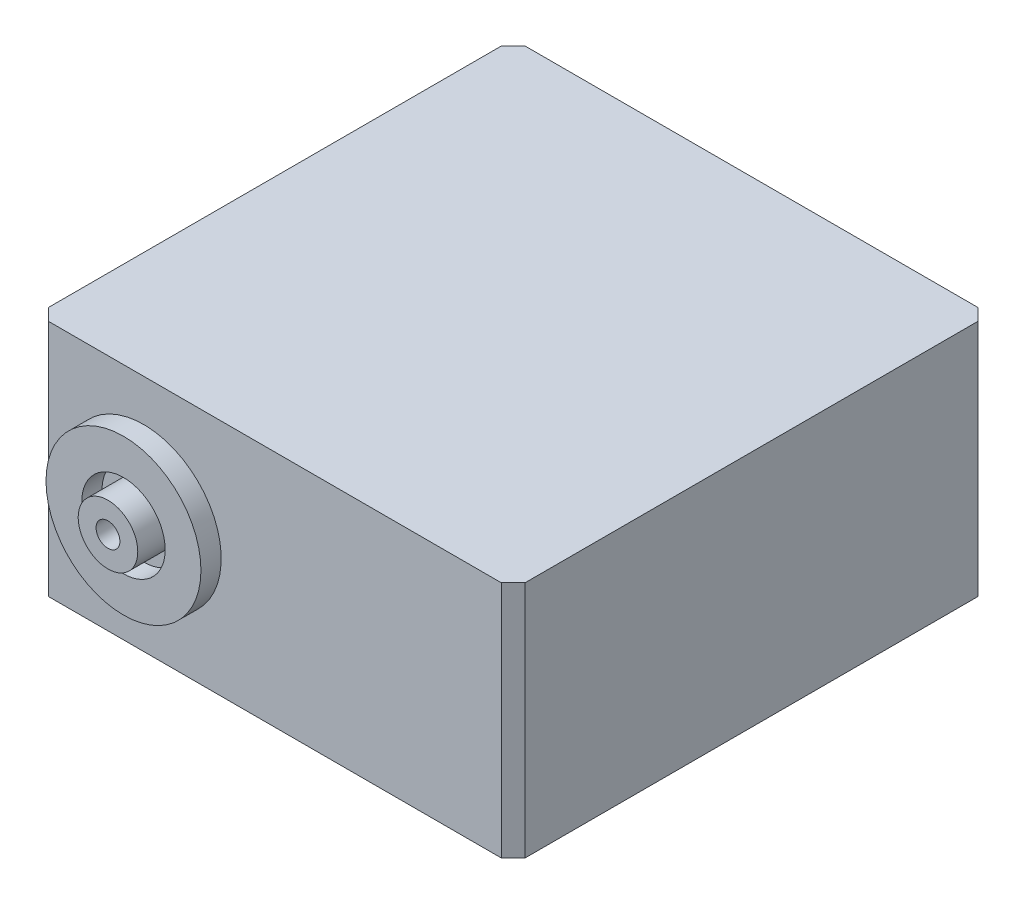
SolidWorks part; units mm, degrees
ref_plane "前视基准面" through (0, 0, 0) normal (0, 0, 1) x (1, 0, 0)
ref_plane "上视基准面" through (0, 0, 0) normal (0, 1, 0) x (1, 0, 0)
ref_plane "右视基准面" through (0, 0, 0) normal (1, 0, 0) x (0, 0, -1)
sketch "草图1" plane through (0, 0, 0) normal (0, 1, 0) x (1, 0, 0)
  line L0 (-57.6434, 26.1497) -> (-19.6434, 26.1497)
  line L1 (-18.6434, 25.1497) -> (-18.6434, -12.8503)
  line L2 (-19.6434, -13.8503) -> (-57.6434, -13.8503)
  line L3 (-58.6434, -12.8503) -> (-58.6434, 25.1497)
  line L4 (-58.6434, 25.1497) -> (-57.6434, 26.1497)
  line L5 (-19.6434, 26.1497) -> (-18.6434, 25.1497)
  line L6 (-18.6434, -12.8503) -> (-19.6434, -13.8503)
  line L7 (-57.6434, -13.8503) -> (-58.6434, -12.8503)
  point P0 (-58.6434, 26.1497)
  point P1 (-18.6434, 26.1497)
  point P2 (-18.6434, -13.8503)
  point P3 (-58.6434, -13.8503)
extrude "凸台-拉伸1" add sketch "草图1" along normal blind 20
sketch "草图4" plane through (0, 0, -26.1497) normal (0, 0, -1) x (-1, 0, 0)
  circle A0 centre (49.6434, 10) radius 6.5
  circle A1 centre (49.6434, 10) radius 3
extrude "凸台-拉伸2" add sketch "草图4" along normal blind 1.7
sketch "草图5" plane through (0, 0, -26.1497) normal (0, 0, -1) x (-1, 0, 0)
  circle A0 centre (49.6434, 10) radius 3
extrude "凸台-拉伸3" add sketch "草图5" along normal blind 2.7
sketch "草图6" plane through (0, 0, -28.8497) normal (0, 0, -1) x (-1, 0, 0)
  circle A0 centre (49.6434, 10) radius 3.2
extrude "凸台-拉伸4" add sketch "草图6" along normal blind 3
sketch "草图7" plane through (0, 0, -31.8497) normal (0, 0, -1) x (-1, 0, 0)
  circle A0 centre (49.6434, 10) radius 1
extrude "切除-拉伸41" cut sketch "草图7" against normal blind 5.7
sketch "草图8" plane through (0, 0, 13.8503) normal (0, 0, 1) x (1, 0, 0)
  circle A0 centre (-49.6434, 10) radius 6.5
  circle A1 centre (-49.6434, 10) radius 3.5
extrude "凸台-拉伸5" add sketch "草图8" along normal blind 1.7
sketch "草图9" plane through (0, 0, 13.8503) normal (0, 0, 1) x (1, 0, 0)
  circle A0 centre (-49.6434, 10) radius 2.5
extrude "凸台-拉伸6" add sketch "草图9" along normal blind 3
sketch "草图10" plane through (0, 0, 16.8503) normal (0, 0, 1) x (1, 0, 0)
  circle A0 centre (-49.6434, 10) radius 1
extrude "切除-拉伸42" cut sketch "草图10" against normal blind 5
sketch "草图11" plane through (-18.6434, 0, 0) normal (1, 0, 0) x (0, 0, -1)
  circle A0 centre (6.1497, 10) radius 3
  circle A1 centre (11.1497, 15.3353) radius 1
  circle A2 centre (11.1497, 4.6647) radius 1
  circle A3 centre (1.1497, 4.6647) radius 1
  circle A4 centre (1.1497, 15.3353) radius 1
